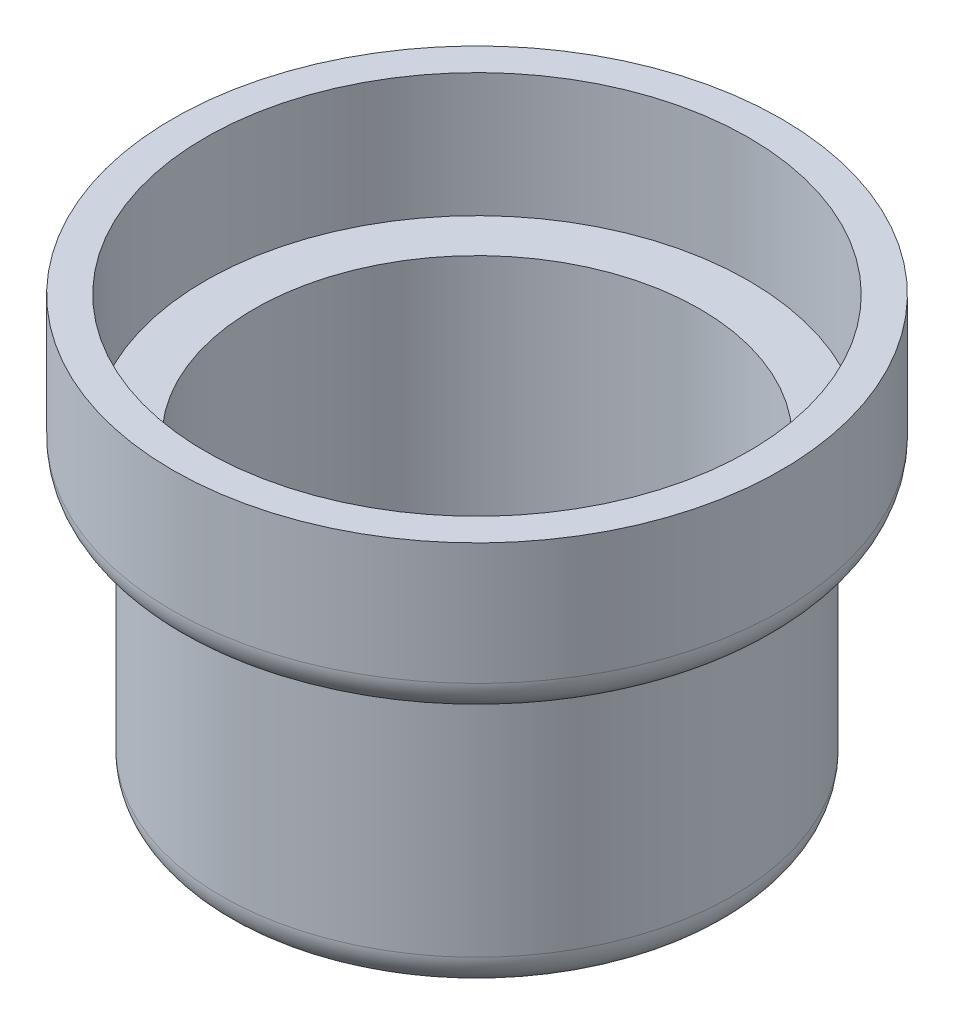
SolidWorks part; units mm, degrees
ref_plane "Front Plane" through (0, 0, 0) normal (0, 0, 1) x (1, 0, 0)
ref_plane "Top Plane" through (0, 0, 0) normal (0, 1, 0) x (1, 0, 0)
ref_plane "Right Plane" through (0, 0, 0) normal (1, 0, 0) x (0, 0, -1)
sketch "Sketch2" plane through (0, 0, 0) normal (0, 0, 1) x (1, 0, 0)
  line L0 (0, 0) -> (0, 34.1974) construction
  line L1 (0, 0) -> (18.6531, 0)
  line L2 (18.6531, 0) -> (18.6531, 19.8438)
  line L3 (18.6531, 19.8438) -> (22.225, 19.8438)
  line L4 (22.225, 19.8438) -> (22.225, 31.2738)
  line L5 (22.225, 31.2738) -> (19.8437, 31.2738)
  line L6 (19.8437, 31.2738) -> (19.8438, 22.225)
  line L7 (19.8438, 22.225) -> (16.2719, 22.225)
  line L8 (16.2719, 22.225) -> (16.2719, 2.3812)
  line L9 (16.2719, 2.3812) -> (0, 2.3812)
  line L10 (0, 0) -> (0, 2.3812)
  point P3 (18.0578, 22.225)
  point P13 (28.2804, 34.1313)
  dimension "D1" = 18.6531
  dimension "D2" = 19.8438
  dimension "D3" = 11.43
  dimension "D4" = 2.3812
  dimension "D5" = 2.3813
  dimension "D6" = 2.3813
  dimension "D7" = 2.3813
  dimension "D8" = 22.225
revolve "Revolve1" add sketch "Sketch2" angle 360 about L0
fillet "Fillet1" radius 2.54 2 edges at (0, 0, -18.6531) (0, 19.8438, -22.225)
